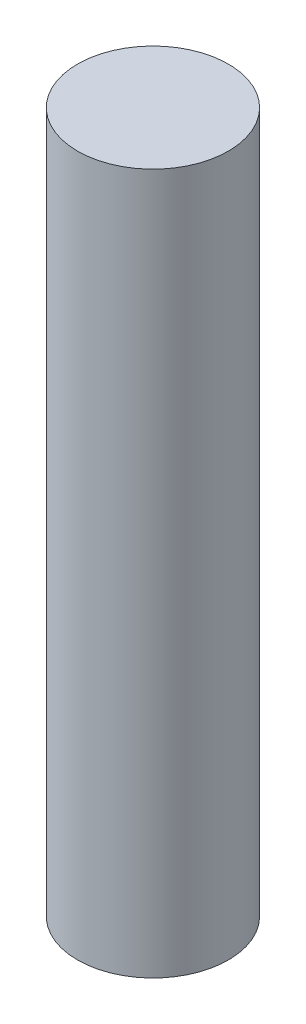
SolidWorks part; units mm, degrees
ref_plane "Front Plane" through (0, 0, 0) normal (0, 0, 1) x (1, 0, 0)
ref_plane "Top Plane" through (0, 0, 0) normal (0, 1, 0) x (1, 0, 0)
ref_plane "Right Plane" through (0, 0, 0) normal (1, 0, 0) x (0, 0, -1)
sketch "Sketch1" plane through (0, 0, 0) normal (0, 1, 0) x (1, 0, 0)
  circle A0 centre (0, 0) radius 1.4
  dimension "2.8" = 2.8
extrude "Boss-Extrude1" add sketch "Sketch1" along normal blind 10
sketch "Sketch2" plane through (0, 10, 0) normal (0, 1, 0) x (1, 0, 0)
  circle A0 centre (0, 0) radius 1.4
  dimension "D1" = 2.8
extrude "Boss-Extrude2" add sketch "Sketch2" along normal blind 3
